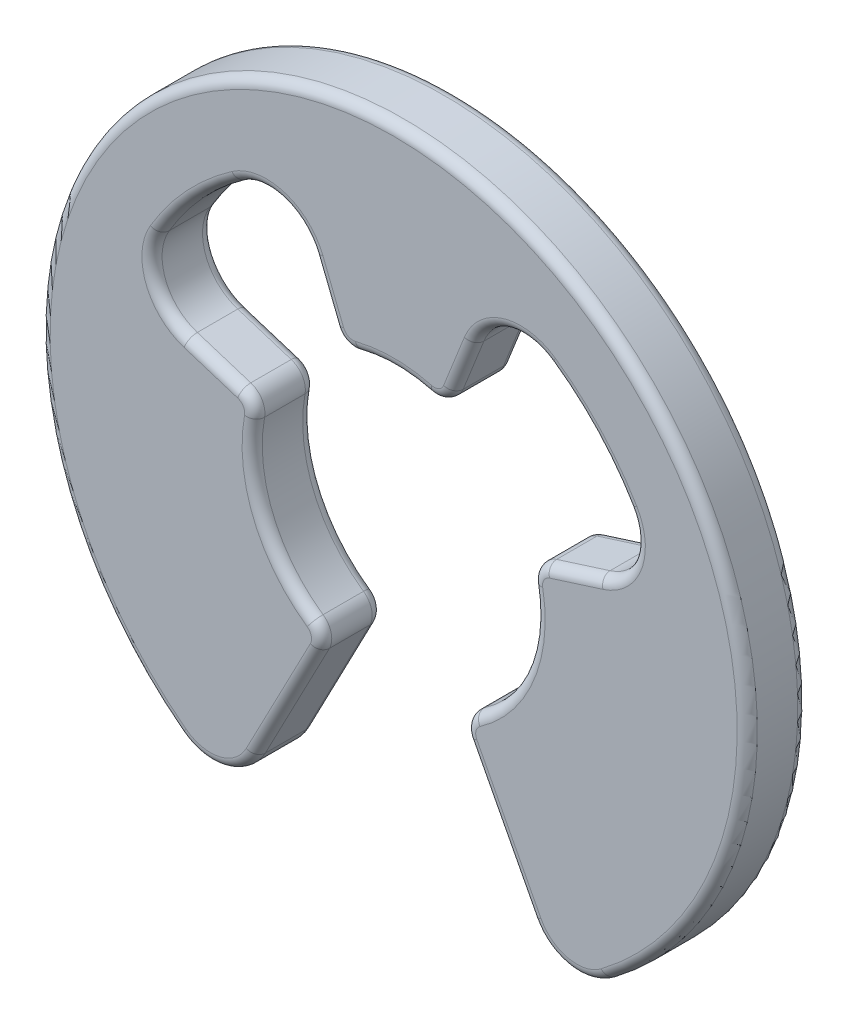
SolidWorks part; units mm, degrees
ref_plane "前视基准面" through (0, 0, 0) normal (0, 0, 1) x (1, 0, 0)
ref_plane "上视基准面" through (0, 0, 0) normal (0, 1, 0) x (1, 0, 0)
ref_plane "右视基准面" through (0, 0, 0) normal (1, 0, 0) x (0, 0, -1)
sketch "草图1" plane through (0, 0, 0) normal (0, 0, 1) x (1, 0, 0)
  line L0 (-0.5185, 1.3004) -> (-1, 2.508)
  line L1 (0.5185, 1.3004) -> (1, 2.508)
  line L2 (-0.6481, -1.2409) -> (-1.6204, -3.1023)
  line L3 (0.6481, -1.2409) -> (1.6204, -3.1023)
  line L4 (-1.3346, 0.4228) -> (-2.5739, 0.8154)
  line L5 (1.3346, 0.4228) -> (2.5739, 0.8154)
  arc A0 (1.6204, -3.1023) -> (-1.6204, -3.1023) centre (0, 0) ccw
  arc A1 (0.6481, -1.2409) -> (1.3346, 0.4228) centre (0, 0) ccw
  circle A2 centre (0, 0) radius 2.7 construction
  arc A3 (-2.5739, 0.8154) -> (-1, 2.508) centre (0, 0) cw
  arc A4 (1, 2.508) -> (2.5739, 0.8154) centre (0, 0) cw
  arc A5 (-1.3346, 0.4228) -> (-0.6481, -1.2409) centre (0, 0) ccw
  arc A6 (0.5185, 1.3004) -> (-0.5185, 1.3004) centre (0, 0) ccw
  point P3 (1.25, -2.3932)
  point P9 (-1.25, -2.3932)
  dimension "D1" = 7
  dimension "D2" = 2.8
  dimension "D4" = 0.8
  dimension "D3" = 2
  dimension "D5" = 2.5
  dimension "D6" = 80
extrude "凸台-拉伸1" add sketch "草图1" along normal blind 0.6
fillet "圆角1" radius 0.2 6 edges at (0.6481, -1.2409, 0.3) (1.3346, 0.4228, 0.3) (0.5185, 1.3004, 0.3) (-0.5185, 1.3004, 0.3) (-1.3346, 0.4228, 0.3) (-0.6481, -1.2409, 0.3)
fillet "圆角2" radius 0.5 6 edges at (1.6204, -3.1023, 0.3) (-1.6204, -3.1023, 0.3) (2.5739, 0.8154, 0.3) (1, 2.508, 0.3) (-2.5739, 0.8154, 0.3) (-1, 2.508, 0.3)
fillet "圆角3" radius 0.1 48 edges at (-0.718, -1.2667, 0) (-1.0522, -2.0145, 0) (-1.7034, -2.8784, 0) (0, 3.5, 0) (1.7034, -2.8784, 0) (1.0522, -2.0145, 0) (0.718, -1.2667, 0) (1.2942, -0.534, 0) (1.4023, 0.3918, 0) (1.7779, 0.5632, 0) (2.3586, 0.9457, 0) (1.9772, 1.8386, 0) (1.1143, 2.2838, 0) (0.6907, 1.7323, 0) (0.4925, 1.3702, 0) (0, 1.4, 0) (-0.4925, 1.3702, 0) (-0.6907, 1.7323, 0) (-1.1143, 2.2838, 0) (-1.9772, 1.8386, 0) (-2.3586, 0.9457, 0) (-1.7779, 0.5632, 0) (-1.4023, 0.3918, 0) (-0.718, -1.2667, 0.6) (-1.0522, -2.0145, 0.6) (-1.7034, -2.8784, 0.6) (0, 3.5, 0.6) (1.7034, -2.8784, 0.6) (1.0522, -2.0145, 0.6) (0.718, -1.2667, 0.6) (1.2942, -0.534, 0.6) (1.4023, 0.3918, 0.6) (1.7779, 0.5632, 0.6) (2.3586, 0.9457, 0.6) (1.9772, 1.8386, 0.6) (1.1143, 2.2838, 0.6) (0.6907, 1.7323, 0.6) (0.4925, 1.3702, 0.6) (0, 1.4, 0.6) (-0.4925, 1.3702, 0.6) (-0.6907, 1.7323, 0.6) (-1.1143, 2.2838, 0.6) (-1.9772, 1.8386, 0.6) (-2.3586, 0.9457, 0.6) (-1.7779, 0.5632, 0.6) (-1.4023, 0.3918, 0.6) (-1.2942, -0.534, 0) (-1.2942, -0.534, 0.6)
